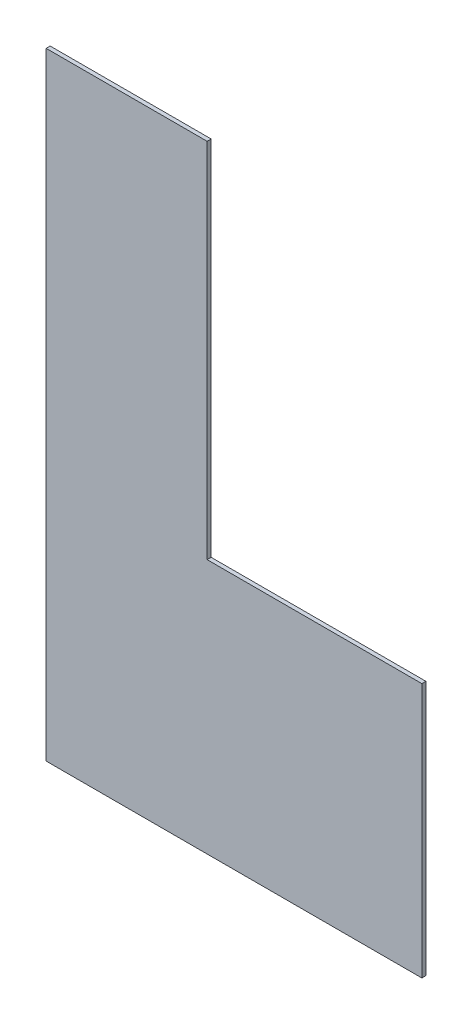
SolidWorks part; units mm, degrees
ref_plane "Plan de face" through (0, 0, 0) normal (0, 0, 1) x (1, 0, 0)
ref_plane "Plan de dessus" through (0, 0, 0) normal (0, 1, 0) x (1, 0, 0)
ref_plane "Plan de droite" through (0, 0, 0) normal (1, 0, 0) x (0, 0, -1)
sketch "Esquisse1" plane through (0, 0, 0) normal (0, 0, 1) x (1, 0, 0)
  line L0 (-158.4145, -408.6715) -> (121.5855, -408.6715)
  line L1 (-158.4145, 51.3285) -> (-38.4145, 51.3285)
  line L2 (-158.4145, 51.3285) -> (-158.4145, -408.6715)
  line L5 (-38.4145, -218.6715) -> (121.5855, -218.6715)
  line L6 (-38.4145, 51.3285) -> (-38.4145, -218.6715)
  line L10 (121.5855, -218.6715) -> (121.5855, -408.6715)
  dimension "D2" = 120
  dimension "D1" = 460
  dimension "D3" = 270
  dimension "D4" = 280
extrude "Boss.-Extru.1" add sketch "Esquisse1" along normal blind 3
equation "\"ProfondeurBoite\"=460"
equation "\"D1@Esquisse1\"=\"ProfondeurBoite\""
equation "\"LongueurSyphon\"=270"
equation "\"D3@Esquisse1\"= \"LongueurSyphon\""
equation "\"LargeurSyphon\"=120"
equation "\"D4@Esquisse1\"= \"LargeurBoite\""
equation "\"EpaisseurPlaque\"= 3"
equation "\"HauteurSyphon\"=\"HauteurCoteGauche\"-\"HauteurSolSyphon\""
equation "\"D1@Boss.-Extru.1\"=\"EpaisseurPlaque\""
equation "\"HauteurCoteDroit\"= 490"
equation "\"HauteurCoteGauche\"= 540"
equation "\"HauteurSolSyphon\"= 300"
equation "\"LargeurDroite\"=10"
equation "\"LargeurGauche\"=150"
equation "\"LargeurBoite\"= \"LargeurDroite\" + \"LargeurGauche\" + \"LargeurSyphon\""
equation "\"D2@Esquisse1\"=\"LargeurGauche\" - 30"
